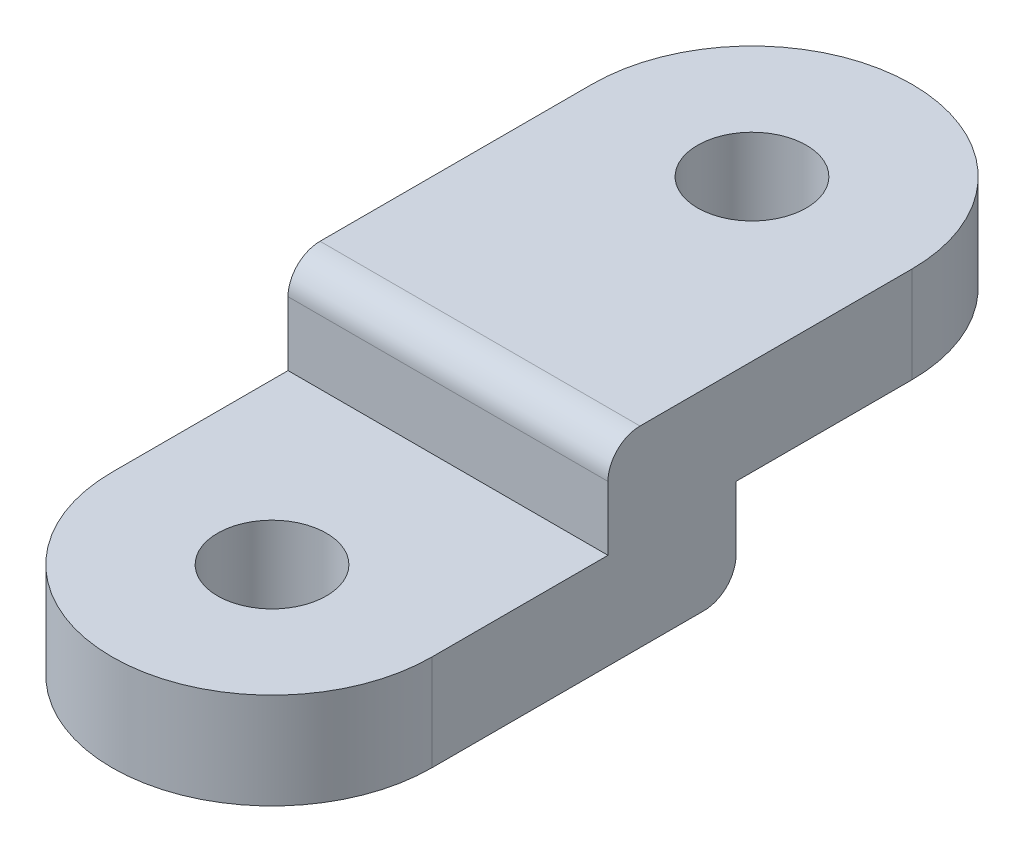
SolidWorks part; units mm, degrees
ref_plane "Plan de face" through (0, 0, 0) normal (0, 0, 1) x (1, 0, 0)
ref_plane "Plan de dessus" through (0, 0, 0) normal (0, 1, 0) x (1, 0, 0)
ref_plane "Plan de droite" through (0, 0, 0) normal (1, 0, 0) x (0, 0, -1)
sketch "Esquisse1" plane through (0, 0, 0) normal (0, 1, 0) x (1, 0, 0)
  line L0 (0, 0) -> (0, 30)
  line L1 (20, 30) -> (20, 0)
  arc A0 (20, 30) -> (0, 30) centre (10, 30) ccw
  arc A1 (0, 0) -> (20, 0) centre (10, 0) ccw
  dimension "D1" = 20
  dimension "D2" = 30
extrude "Boss.-Extru.1" add sketch "Esquisse1" along normal blind 6
sketch "Esquisse7" plane through (0, 6, 0) normal (0, 1, 0) x (1, 0, 0)
  arc A0 (20, 30) -> (0, 30) centre (10, 30) ccw construction
  arc A1 (0, 0) -> (20, 0) centre (10, 0) ccw construction
  point P0 (10, 30)
  point P5 (10, 0)
sketch "Esquisse12" plane through (0, 0, 0) normal (0, -1, 0) x (1, 0, 0)
  line L0 (0, -30) -> (20, -30)
  line L1 (0, -30) -> (0, 0) construction
  line L2 (20, 0) -> (20, -30) construction
  line L3 (20, -30) -> (20, 0)
  line L4 (0, 0) -> (0, -30)
  arc A0 (20, 0) -> (0, 0) centre (10, 0) ccw construction
  arc A1 (20, 0) -> (0, 0) centre (10, 0) ccw
extrude "Boss.-Extru.2" add sketch "Esquisse12" along normal blind 12
sketch "Esquisse14" plane through (20, 0, 0) normal (1, 0, 0) x (0, 0, -1)
  line L0 (11, 6) -> (11, 0)
  line L1 (0, 6) -> (30, 6) construction
  line L2 (11, 0) -> (-10, 0)
  line L3 (-10, 6) -> (-10, -12) construction
  line L4 (-10, 0) -> (-10, 6)
  line L5 (-10, 6) -> (11, 6)
  line L6 (30, 0) -> (40, 0) construction
  line L7 (15, 10.1399) -> (15, -19.2589) construction
  line L10 (0, 6) -> (0, -12) construction
  line L11 (30, 6) -> (30, 0) construction
  line L12 (30, 0) -> (19, 0)
  line L13 (19, 0) -> (19, -6)
  line L14 (19, -6) -> (-10, -6)
  line L15 (-10, -6) -> (-10, -12)
  line L16 (-10, -12) -> (0, -12) construction
  line L17 (-10, -12) -> (30, -12)
  line L18 (30, -12) -> (30, 0)
  dimension "D1" = 4
  dimension "D2" = 6
  dimension "D3" = 8
extrude "Enlèv. mat.-Extru.2" cut sketch "Esquisse14" against normal through all
hole_wizard "Trou taraudé M81" positions "Esquisse15" profile "Esquisse16" tap size "M8" standard "ISO" end condition through all
sketch "Esquisse15" plane through (0, 6, 0) normal (0, 1, 0) x (1, 0, 0)
  point P0 (10, 30)
cosmetic thread "Filetage de perçage12" parameters "D2"=8
sketch "Esquisse16" plane through (10, 6, -30) normal (1, 0, 0) x (0, 0, 1)
  line L0 (0, 0) -> (0, 12)
  line L1 (0, 12) -> (3.4, 12)
  line L2 (3.4, 12) -> (3.4, 0)
  line L5 (3.4, 0) -> (0, 0)
  line L11 (0, -6.35) -> (0, 107.95) construction
  dimension "Diamètre du trou pour taraudage jusqu'au prochain" = 6.8
  dimension "Profondeur du trou pour taraudage jusqu'au prochain" = 12
hole_wizard "Trou taraudé M82" positions "Esquisse17" profile "Esquisse18" tap size "M8" standard "ISO" end condition through all
sketch "Esquisse17" plane through (0, 0, 0) normal (0, 1, 0) x (1, 0, 0)
  arc A0 (0, 0) -> (20, 0) centre (10, 0) ccw construction
  point P0 (10, 0)
cosmetic thread "Filetage de perçage13" parameters "D2"=8
sketch "Esquisse18" plane through (10, 0, 0) normal (1, 0, 0) x (0, 0, 1)
  line L0 (0, 0) -> (0, 6)
  line L1 (0, 6) -> (3.4, 6)
  line L2 (3.4, 6) -> (3.4, 0)
  line L5 (3.4, 0) -> (0, 0)
  line L11 (0, -6.35) -> (0, 107.95) construction
  dimension "Diamètre du trou pour taraudage jusqu'au prochain" = 6.8
  dimension "Profondeur du trou pour taraudage jusqu'au prochain" = 6
fillet "Congé1" radius 2 2 edges at (10, 6, -11) (10, -6, -19)
